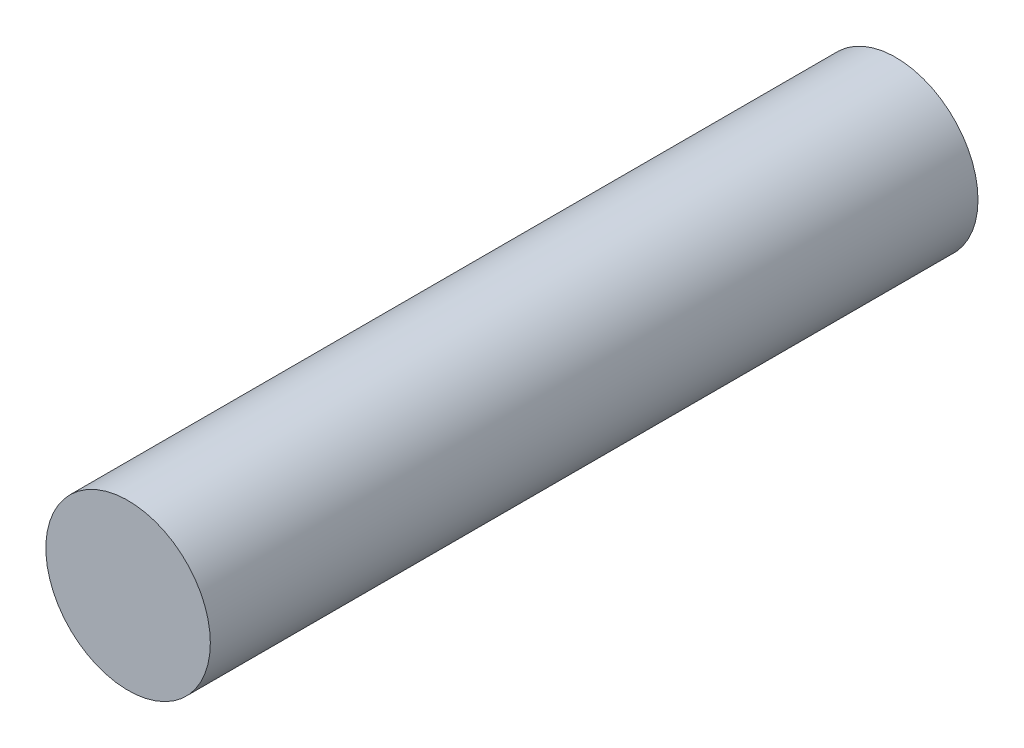
SolidWorks part; units mm, degrees
ref_plane "Front Plane" through (0, 0, 0) normal (0, 0, 1) x (1, 0, 0)
ref_plane "Top Plane" through (0, 0, 0) normal (0, 1, 0) x (1, 0, 0)
ref_plane "Right Plane" through (0, 0, 0) normal (1, 0, 0) x (0, 0, -1)
sketch "Sketch1" plane through (0, 0, 0) normal (0, 0, 1) x (1, 0, 0)
  circle A0 centre (0, 0) radius 1.5
  dimension "D1" = 3
extrude "Boss-Extrude1" add sketch "Sketch1" along normal blind 14
